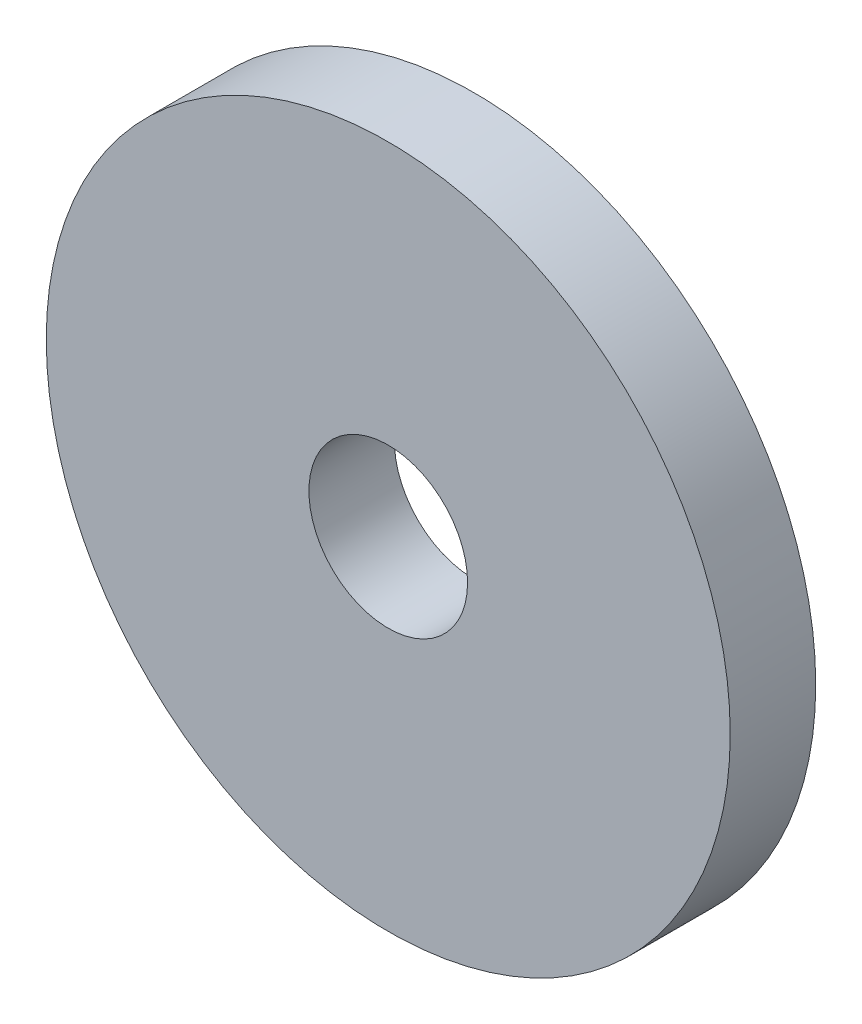
SolidWorks part; units mm, degrees
ref_plane "Front Plane" through (0, 0, 0) normal (0, 0, 1) x (1, 0, 0)
ref_plane "Top Plane" through (0, 0, 0) normal (0, 1, 0) x (1, 0, 0)
ref_plane "Right Plane" through (0, 0, 0) normal (1, 0, 0) x (0, 0, -1)
sketch "Sketch1" plane through (0, 0, 0) normal (0, 0, 1) x (1, 0, 0)
  circle A0 centre (0, 0) radius 6.35
  circle A1 centre (0, 0) radius 1.4732
  dimension "D1" = 12.7
  dimension "D2" = 2.9464
extrude "Boss-Extrude1" add sketch "Sketch1" along normal blind 1.5875
